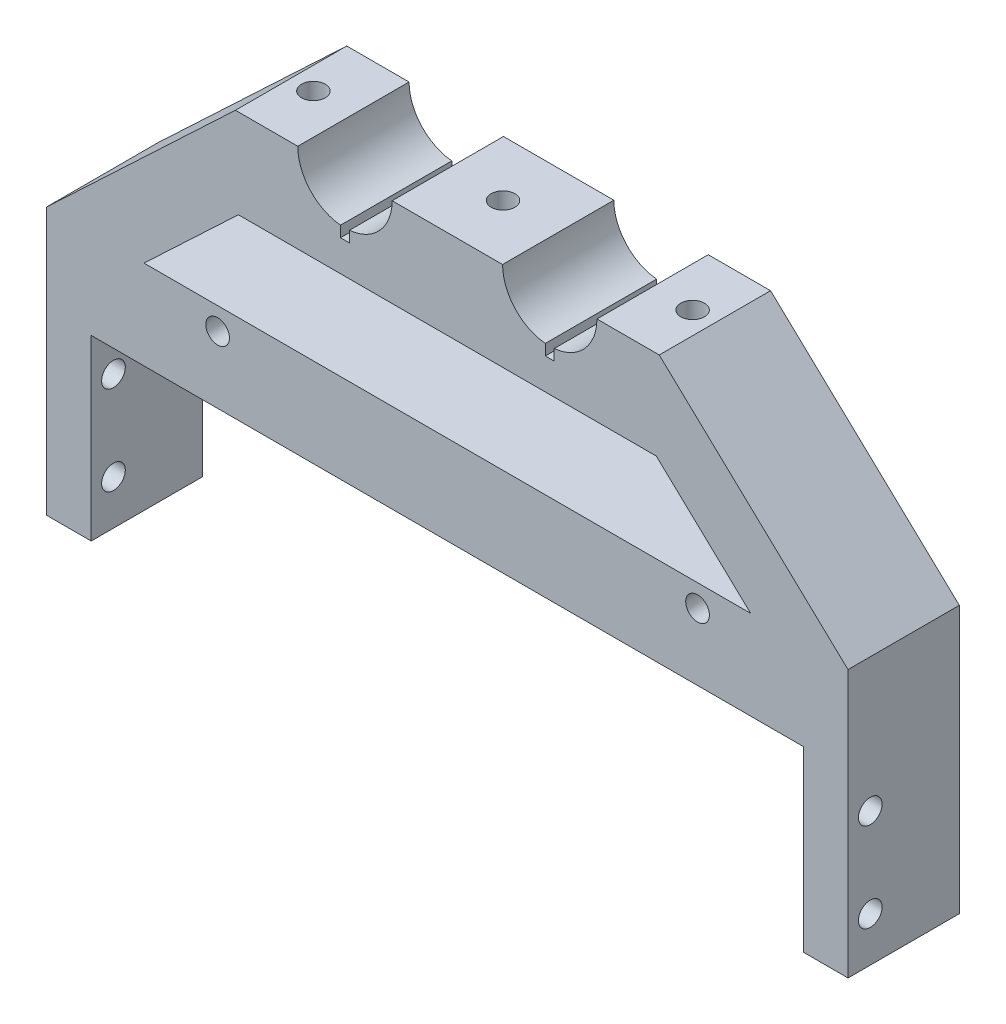
SolidWorks part; units mm, degrees
ref_plane "Front Plane" through (0, 0, 0) normal (0, 0, 1) x (1, 0, 0)
ref_plane "Top Plane" through (0, 0, 0) normal (0, 1, 0) x (1, 0, 0)
ref_plane "Right Plane" through (0, 0, 0) normal (1, 0, 0) x (0, 0, -1)
sketch "Sketch2" plane through (0, 0, 0) normal (0, 0, 1) x (1, 0, 0)
  line L0 (215.9, 0) -> (228.6, 0)
  line L4 (228.6, 0) -> (228.6, 101.6)
  line L9 (12.7, 0) -> (0, 0)
  line L10 (0, 0) -> (0, 101.6)
  line L12 (0, 101.6) -> (53.848, 152.4)
  line L13 (228.6, 101.6) -> (174.752, 152.4)
  line L14 (53.848, 152.4) -> (71.628, 152.4)
  line L15 (98.552, 152.4) -> (130.048, 152.4)
  line L16 (12.7, 0) -> (12.7, 76.2)
  line L17 (12.7, 76.2) -> (215.9, 76.2)
  line L18 (215.9, 76.2) -> (215.9, 0)
  line L19 (156.972, 152.4) -> (174.752, 152.4)
  arc A3 (71.628, 152.4) -> (98.552, 152.4) centre (85.09, 152.4) ccw
  arc A4 (130.048, 152.4) -> (156.972, 152.4) centre (143.51, 152.4) ccw
  dimension "D3" = 12.7
  dimension "D6" = 53.848
  dimension "D7" = 13.462
  dimension "D15" = 17.78
  dimension "D5" = 26.924
  dimension "D2" = 12.7
  dimension "D4" = 228.6
  dimension "D8" = 85.09
  dimension "D9" = 85.09
  dimension "D10" = 101.6
  dimension "D11" = 50.8
  dimension "D12" = 76.2
  dimension "D13" = 101.6
  dimension "D14" = 203.2
  dimension "D16" = 50.8
  dimension "D17" = 152.4
  dimension "D18" = 152.4
  dimension "D19" = 152.4
extrude "Boss-Extrude1" add sketch "Sketch2" along normal blind 50.8
sketch "Sketch3" plane through (0, 0, 0) normal (-1, 0, 0) x (0, 0, 1)
  line L2 (50.8, 0) -> (0, 0) construction
  circle A0 centre (25.4, 63.5) radius 3.3782
  circle A1 centre (25.4, 38.1) radius 3.3782
  dimension "D1" = 6.7564
  dimension "D2" = 6.7564
  dimension "D3" = 38.1
  dimension "D4" = 25.4
extrude "Cut-Extrude1" cut sketch "Sketch3" against normal blind 25.4
sketch "Sketch4" plane through (228.6, 0, 0) normal (1, 0, 0) x (0, 0, -1)
  line L1 (-50.8, 0) -> (0, 0) construction
  circle A0 centre (-25.4, 63.5) radius 3.3782
  circle A1 centre (-25.4, 38.1) radius 3.3782
  dimension "D1" = 6.7564
  dimension "D2" = 6.7564
  dimension "D5" = 38.1
  dimension "D6" = 63.5
extrude "Cut-Extrude2" cut sketch "Sketch4" against normal blind 25.4
sketch "Sketch7" plane through (0, 0, 50.8) normal (0, 0, 1) x (1, 0, 0)
  line L0 (228.6, 0) -> (228.6, 101.6) construction
  line L1 (0, 0) -> (228.6, 0)
  line L2 (0, 0) -> (0, 152.4)
  line L3 (0, 152.4) -> (228.6, 152.4)
  line L4 (228.6, 0) -> (228.6, 152.4)
  line L5 (130.048, 152.4) -> (98.552, 152.4) construction
extrude "Cut-Extrude5" cut sketch "Sketch7" against normal blind 19.05
sketch "Sketch8" plane through (0, 0, 31.75) normal (0, 0, 1) x (1, 0, 0)
  line L0 (0, 0) -> (0, 101.6) construction
  line L1 (0, 25.4) -> (228.6, 25.4)
  line L2 (0, 25.4) -> (0, 0)
  line L3 (0, 0) -> (228.6, 0)
  line L4 (228.6, 25.4) -> (228.6, 0)
  dimension "D1" = 25.4
extrude "Cut-Extrude6" cut sketch "Sketch8" against normal blind 39.37
sketch "Sketch9" plane through (0, 152.4, 0) normal (0, 1, 0) x (1, 0, 0)
  line L1 (71.628, 0) -> (53.848, 0) construction
  line L2 (130.048, 0) -> (98.552, 0) construction
  line L3 (114.3, 27.6941) -> (114.3, -48.8787) construction
  line L5 (174.752, -31.75) -> (174.752, 0) construction
  line L6 (53.848, -31.75) -> (53.848, 0) construction
  circle A0 centre (60.198, -15.875) radius 3.3782
  circle A1 centre (114.3, -15.875) radius 3.3782
  circle A2 centre (168.402, -15.875) radius 3.3782
  dimension "D1" = 6.7564
  dimension "D2" = 6.7564
  dimension "D3" = 6.35
  dimension "D4" = 15.875
  dimension "D5" = 15.875
  dimension "D6" = 60.452
extrude "Cut-Extrude7" cut sketch "Sketch9" against normal blind 27.94
sketch "Sketch10" plane through (0, 0, 31.75) normal (0, 0, 1) x (1, 0, 0)
  line L7 (27.7608, 101.6) -> (54.6848, 127)
  line L8 (54.6848, 127) -> (173.9152, 127)
  line L9 (27.7608, 101.6) -> (200.8392, 101.6)
  line L10 (0, 101.6) -> (53.848, 152.4) construction
  line L11 (173.9152, 127) -> (200.8392, 101.6)
  line L12 (174.752, 152.4) -> (228.6, 101.6) construction
  line L13 (98.552, 152.4) -> (130.048, 152.4) construction
  dimension "D1" = 25.4
  dimension "D2" = 19.05
  dimension "D3" = 19.05
  dimension "D4" = 25.4
extrude "Cut-Extrude8" cut sketch "Sketch10" against normal blind 40.64
sketch "Sketch12" plane through (0, 152.4, 0) normal (0, 1, 0) x (1, 0, 0)
  line L0 (85.09, -31.75) -> (85.09, 0)
  line L1 (71.628, -31.75) -> (98.552, -31.75) construction
  line L2 (98.552, 0) -> (71.628, 0) construction
  line L3 (85.09, 0) -> (86.36, 0)
  line L4 (86.36, 0) -> (86.36, -31.75)
  line L5 (86.36, -31.75) -> (83.82, -31.75)
  line L6 (83.82, -31.75) -> (83.82, 0)
  line L7 (83.82, 0) -> (85.09, 0)
  line L8 (114.3, 104.6898) -> (114.3, -104.6898) construction
  line L9 (130.048, 0) -> (98.552, 0) construction
  line L10 (144.78, 0) -> (143.51, 0)
  line L11 (144.78, -31.75) -> (144.78, 0)
  line L12 (142.24, -31.75) -> (144.78, -31.75)
  line L13 (142.24, 0) -> (142.24, -31.75)
  line L14 (143.51, 0) -> (142.24, 0)
  line L15 (143.51, -31.75) -> (143.51, 0)
  point P14 (114.3, 0)
  dimension "D1" = 1.27
  dimension "D2" = 1.27
extrude "Cut-Extrude9" cut sketch "Sketch12" against normal blind 16.51 contours L5 L4 L3 L0 | L7 L6 L5 L0 | L14 L13 L12 L11 L10
sketch "Sketch13" plane through (0, 0, 31.75) normal (0, 0, 1) x (1, 0, 0)
  line L1 (27.7608, 101.6) -> (200.8392, 101.6) construction
  line L2 (0, 25.4) -> (0, 101.6) construction
  circle A0 centre (48.768, 95.25) radius 3.3782
  circle A1 centre (185.674, 95.25) radius 3.3782
  dimension "D1" = 6.7564
  dimension "D2" = 6.7564
  dimension "D3" = 6.35
  dimension "D4" = 6.35
  dimension "D5" = 48.768
  dimension "D6" = 185.674
extrude "Cut-Extrude10" cut sketch "Sketch13" against normal up to next
